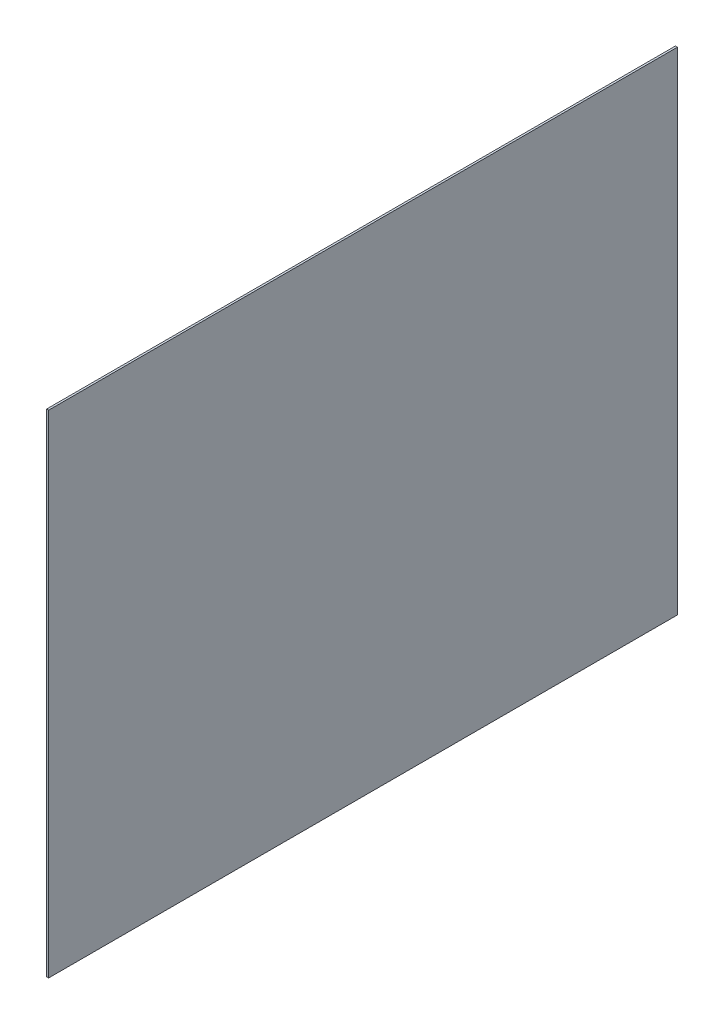
SolidWorks part; units mm, degrees
material "Oak"
ref_plane "Front Plane" through (0, 0, 0) normal (0, 0, 1) x (1, 0, 0)
ref_plane "Top Plane" through (0, 0, 0) normal (0, 1, 0) x (1, 0, 0)
ref_plane "Right Plane" through (0, 0, 0) normal (1, 0, 0) x (0, 0, -1)
sketch "Sketch1" plane through (0, 0, 0) normal (1, 0, 0) x (0, 0, -1)
  line L1 (-3962.4, -3098.8) -> (3962.4, -3098.8)
  line L2 (-3962.4, -3098.8) -> (-3962.4, 3098.8)
  line L3 (-3962.4, 3098.8) -> (3962.4, 3098.8)
  line L4 (3962.4, -3098.8) -> (3962.4, 3098.8)
  line L5 (-3962.4, -3098.8) -> (3962.4, 3098.8) construction
  line L6 (-3962.4, 3098.8) -> (3962.4, -3098.8) construction
  point P0 (0, 0)
  dimension "D1" = 6197.6
  dimension "D2" = 7924.8
extrude "Boss-Extrude1" add sketch "Sketch1" along normal blind 25.4
equation "\"D1@Sketch1\"=220in+24in"
equation "\"D2@Sketch1\"=288in+24in"
equation "\"D1@Boss-Extrude1\"=1"
